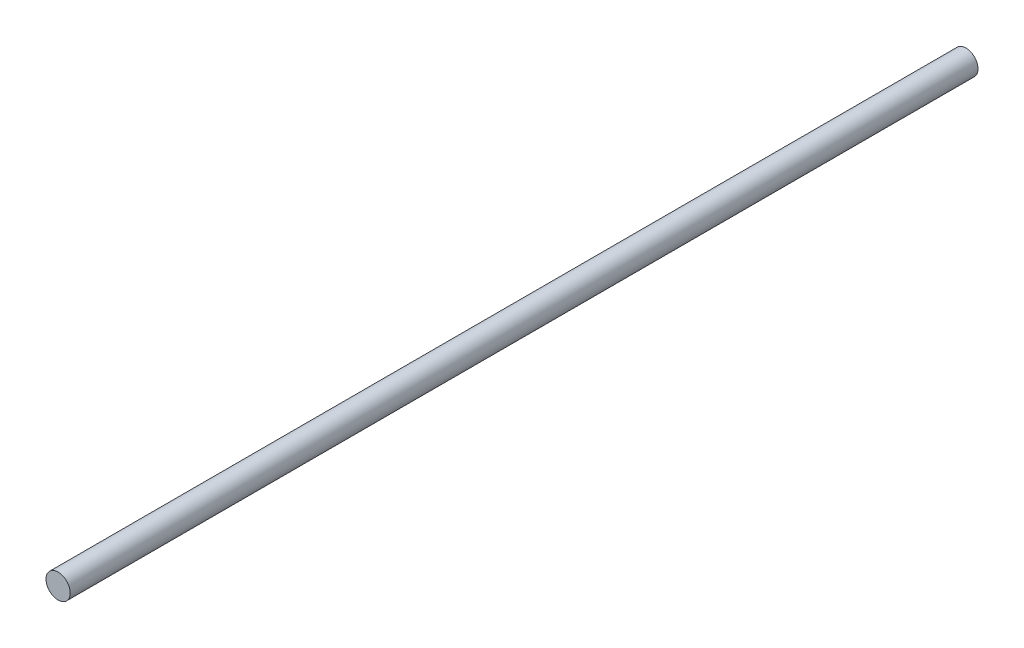
SolidWorks part; units mm, degrees
ref_plane "Front Plane" through (0, 0, 0) normal (0, 0, 1) x (1, 0, 0)
ref_plane "Top Plane" through (0, 0, 0) normal (0, 1, 0) x (1, 0, 0)
ref_plane "Right Plane" through (0, 0, 0) normal (1, 0, 0) x (0, 0, -1)
sketch "Sketch1" plane through (0, 0, 0) normal (0, 0, 1) x (1, 0, 0)
  circle A0 centre (0, 0) radius 4
  dimension "D1" = 8
extrude "Boss-Extrude1" add sketch "Sketch1" along normal blind 300 contours A0
